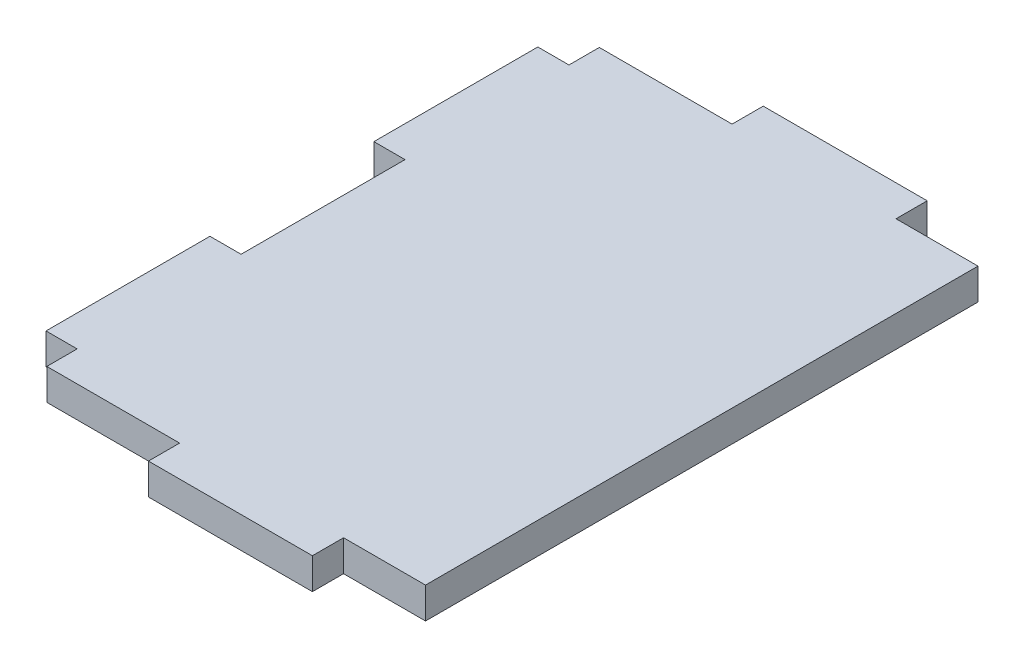
SolidWorks part; units mm, degrees
material "1060 Alloy"
ref_plane "Front Plane" through (0, 0, 0) normal (0, 0, 1) x (1, 0, 0)
ref_plane "Top Plane" through (0, 0, 0) normal (0, 1, 0) x (1, 0, 0)
ref_plane "Right Plane" through (0, 0, 0) normal (1, 0, 0) x (0, 0, -1)
sketch "Sketch1" plane through (0, 0, 0) normal (0, 1, 0) x (1, 0, 0)
  line L0 (4.826, 60.325) -> (4.826, 34.925)
  line L1 (0, 0) -> (63.5, 0) construction
  line L2 (0, 0) -> (0, 95.25) construction
  line L3 (0, 95.25) -> (63.5, 95.25) construction
  line L4 (63.5, 0) -> (63.5, 95.25) construction
  line L5 (4.826, 90.424) -> (25.4, 90.424)
  line L6 (4.826, 90.424) -> (4.826, 85.725)
  line L7 (4.826, 4.826) -> (25.4, 4.826)
  line L8 (63.5, 90.424) -> (63.5, 4.826)
  line L9 (0, 47.625) -> (4.826, 47.625) construction
  line L10 (50.8, 4.826) -> (50.8, 0)
  line L11 (50.8, 0) -> (25.4, 0)
  line L12 (25.4, 4.826) -> (25.4, 0)
  line L13 (4.826, 9.525) -> (0, 9.525)
  line L15 (4.826, 34.925) -> (0, 34.925)
  line L16 (0, 9.525) -> (0, 34.925)
  line L17 (4.826, 60.325) -> (0, 60.325)
  line L19 (4.826, 85.725) -> (0, 85.725)
  line L20 (0, 60.325) -> (0, 85.725)
  line L22 (25.4, 90.424) -> (25.4, 95.25)
  line L23 (25.4, 95.25) -> (50.8, 95.25)
  line L24 (50.8, 90.424) -> (50.8, 95.25)
  line L25 (4.826, 9.525) -> (4.826, 4.826)
  line L26 (50.8, 90.424) -> (63.5, 90.424)
  line L27 (50.8, 4.826) -> (63.5, 4.826)
  dimension "D1" = 95.25
  dimension "D2" = 63.5
  dimension "D3" = 4.826
  dimension "D4" = 25.4
  dimension "D5" = 25.4
  dimension "D6" = 25.4
extrude "Boss-Extrude1" add sketch "Sketch1" along normal blind 4.826
equation "\"sheet width\"= .19"
equation "\"width\"= 24.5"
equation "\"length\"= 34.5"
equation "\"standoff hole size\"= .5"
equation "\"ground clearence\"= 3"
equation "\"small drive pulley\"= 74.55mm"
equation "\"large drive pulley\"= 150.95mm"
equation "\"drive axle hole size\"= .5"
equation "\"front pulley clearence\"= 1"
equation "\"center support location\"= 19"
equation "\"inner to outer wall size\"= 3.75"
equation "\"D1@Sketch1\"=\"inner to outer wall size\""
equation "\"D3@Sketch1\"=\"sheet width\""
equation "\"D1@Boss-Extrude1\"=\"sheet width\""
